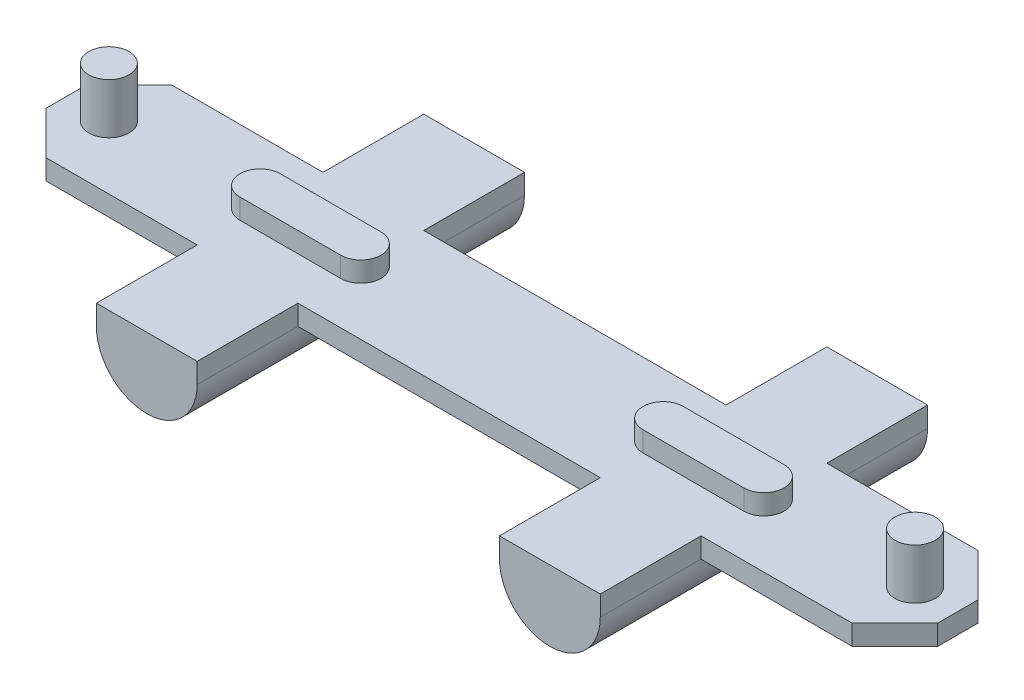
SolidWorks part; units mm, degrees
ref_plane "Alzado" through (0, 0, 0) normal (0, 0, 1) x (1, 0, 0)
ref_plane "Planta" through (0, 0, 0) normal (0, 1, 0) x (1, 0, 0)
ref_plane "Vista lateral" through (0, 0, 0) normal (1, 0, 0) x (0, 0, -1)
sketch "Croquis1" plane through (0, 0, 0) normal (0, 1, 0) x (1, 0, 0)
  line L24 (0, 0) -> (0, 4)
  line L25 (0, 4) -> (4.2426, 8.2426)
  line L26 (4.2426, 8.2426) -> (19.2426, 8.2426)
  line L27 (19.2426, 8.2426) -> (19.2426, 18.2426)
  line L28 (19.2426, 18.2426) -> (29.2426, 18.2426)
  line L29 (29.2426, 18.2426) -> (29.2426, 8.2426)
  line L30 (29.2426, 8.2426) -> (59.2426, 8.2426)
  line L31 (0, 0) -> (4.2426, -4.2426)
  line L32 (4.2426, -4.2426) -> (19.2426, -4.2426)
  line L33 (19.2426, -4.2426) -> (19.2426, -14.2426)
  line L34 (19.2426, -14.2426) -> (29.2426, -14.2426)
  line L35 (29.2426, -14.2426) -> (29.2426, -4.2426)
  line L36 (29.2426, -4.2426) -> (59.2426, -4.2426)
  line L37 (44.2426, 25.1561) -> (44.2426, -18.3658) construction
  line L38 (59.2426, -14.2426) -> (59.2426, -4.2426)
  line L39 (69.2426, -14.2426) -> (59.2426, -14.2426)
  line L40 (69.2426, -4.2426) -> (69.2426, -14.2426)
  line L41 (84.2426, -4.2426) -> (69.2426, -4.2426)
  line L42 (88.4853, 0) -> (84.2426, -4.2426)
  line L43 (59.2426, 18.2426) -> (59.2426, 8.2426)
  line L44 (69.2426, 18.2426) -> (59.2426, 18.2426)
  line L45 (69.2426, 8.2426) -> (69.2426, 18.2426)
  line L46 (84.2426, 8.2426) -> (69.2426, 8.2426)
  line L47 (88.4853, 4) -> (84.2426, 8.2426)
  line L48 (88.4853, 0) -> (88.4853, 4)
  line L49 (0, 2) -> (4.2426, 2) construction
  point P17 (44.2426, -4.2426)
  point P23 (44.2426, 8.2426)
  dimension "D1" = 15
extrude "Saliente-Extruir1" add sketch "Croquis1" along normal blind 2
sketch "Croquis2" plane through (0, 2, 0) normal (0, 1, 0) x (1, 0, 0)
  line L0 (69.2426, 2) -> (59.2426, 2) construction
  line L2 (69.2426, 4) -> (59.2426, 4)
  line L3 (44.2426, 8.2426) -> (44.2426, -4.2426) construction
  line L4 (59.2426, 8.2426) -> (29.2426, 8.2426) construction
  line L5 (29.2426, -4.2426) -> (59.2426, -4.2426) construction
  line L6 (69.2426, 0) -> (59.2426, 0)
  line L8 (19.2426, 2) -> (29.2426, 2) construction
  line L9 (19.2426, 4) -> (29.2426, 4)
  line L10 (19.2426, 0) -> (29.2426, 0)
  arc A1 (19.2426, 4) -> (19.2426, 0) centre (19.2426, 2) ccw
  arc A2 (29.2426, 0) -> (29.2426, 4) centre (29.2426, 2) ccw
  arc A3 (69.2426, 4) -> (69.2426, 0) centre (69.2426, 2) cw
  arc A4 (59.2426, 0) -> (59.2426, 4) centre (59.2426, 2) cw
  point P2 (64.2426, 2)
  point P20 (24.2426, 2)
extrude "Saliente-Extruir3" add sketch "Croquis2" along normal blind 2 contours A4 L6 A3 L2 | L10 A2 L9 A1
sketch "Croquis3" plane through (0, 2, 0) normal (0, 1, 0) x (1, 0, 0)
  line L4 (59.2426, 8.2426) -> (29.2426, 8.2426) construction
  line L5 (44.2426, 8.2426) -> (44.2426, -4.2426) construction
  line L6 (29.2426, -4.2426) -> (59.2426, -4.2426) construction
  circle A0 centre (4.2426, 2) radius 2
  circle A1 centre (84.2426, 2) radius 2
extrude "Saliente-Extruir4" add sketch "Croquis3" along normal blind 5 contours A1 | A0
sketch "Croquis4" plane through (0, 0, 14.2426) normal (0, 0, 1) x (1, 0, 0)
  line L0 (59.2426, 0) -> (69.2426, 0) construction
  line L1 (19.2426, 0) -> (29.2426, 0) construction
  line L4 (19.2426, 0) -> (29.2426, 0)
  line L5 (59.2426, 0) -> (69.2426, 0)
  arc A1 (29.2426, 0) -> (19.2426, 0) centre (24.2426, 0) cw
  arc A2 (69.2426, 0) -> (59.2426, 0) centre (64.2426, 0) cw
extrude "Saliente-Extruir5" add sketch "Croquis4" against normal blind 32.48 contours L5 A2 | L4 A1
